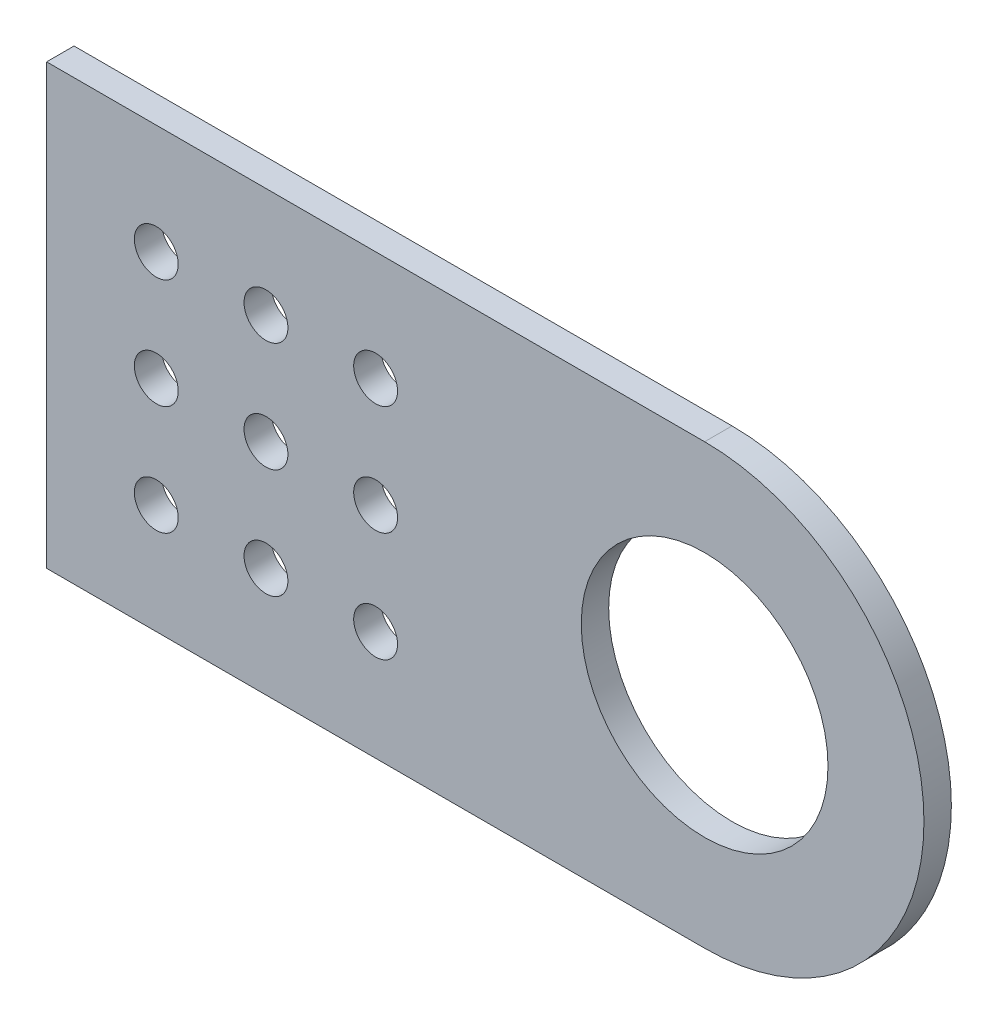
SolidWorks part; units mm, degrees
ref_plane "Front Plane" through (0, 0, 0) normal (0, 0, 1) x (1, 0, 0)
ref_plane "Top Plane" through (0, 0, 0) normal (0, 1, 0) x (1, 0, 0)
ref_plane "Right Plane" through (0, 0, 0) normal (1, 0, 0) x (0, 0, -1)
sketch "Sketch1" plane through (0, 0, 0) normal (0, 0, 1) x (1, 0, 0)
  line L0 (0, 0) -> (0, 50.8)
  line L1 (0, 50.8) -> (76.2, 50.8)
  line L2 (76.2, 0) -> (0, 0)
  line L3 (0, 0) -> (76.2, 0) construction
  arc A0 (76.2, 50.8) -> (76.2, 0) centre (76.2, 25.4) cw
  circle A1 centre (12.7, 38.1) radius 2.54
  circle A2 centre (25.4, 38.1) radius 2.54
  circle A3 centre (38.1, 38.1) radius 2.54
  circle A4 centre (25.4, 25.4) radius 2.54
  circle A5 centre (38.1, 25.4) radius 2.54
  circle A6 centre (25.4, 12.7) radius 2.54
  circle A7 centre (38.1, 12.7) radius 2.54
  circle A8 centre (12.7, 25.4) radius 2.54
  circle A9 centre (12.7, 12.7) radius 2.54
  circle A10 centre (76.2, 25.4) radius 14.2875
  point P8 (0, 0)
  point P9 (0, 0)
  dimension "D3" = 5.08
  dimension "D10" = 28.575
  dimension "D1" = 50.8
  dimension "D2" = 76.2
  dimension "D4" = 12.7
  dimension "D5" = 12.7
  dimension "D8" = 12.7
  dimension "D9" = 12.7
  dimension "D11" = 25.4
  dimension "D6" = 3
  dimension "D7" = 3
extrude "Boss-Extrude1" add sketch "Sketch1" along normal blind 3.175
